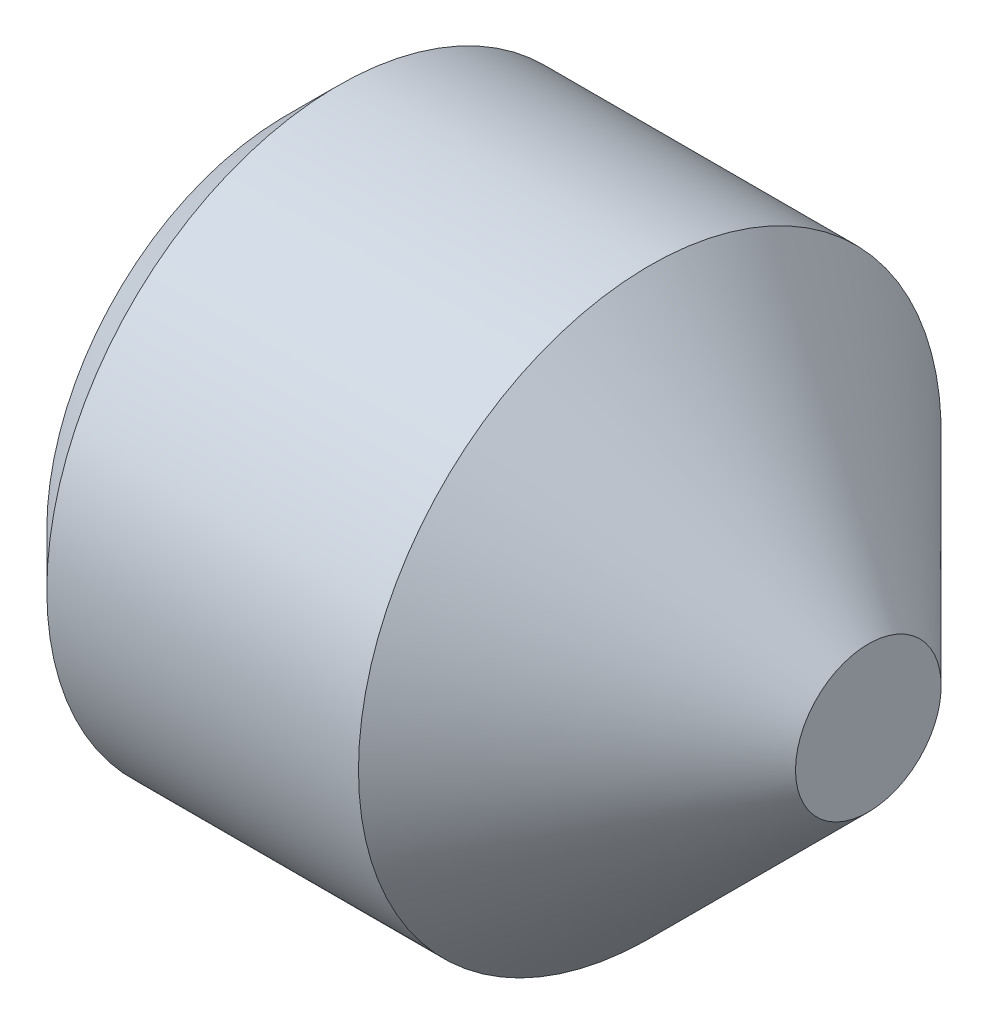
SolidWorks part; units mm, degrees
ref_plane "Front" through (0, 0, 0) normal (0, 0, 1) x (1, 0, 0)
ref_plane "Top" through (0, 0, 0) normal (0, 1, 0) x (1, 0, 0)
ref_plane "Right" through (0, 0, 0) normal (1, 0, 0) x (0, 0, -1)
sketch "Sketch1" plane through (0, 0, 0) normal (0, 0, 1) x (1, 0, 0)
  line L0 (0, 0) -> (3, 0)
  line L1 (3, 0) -> (3, 0.375)
  line L2 (3, 0.375) -> (1.875, 1.5)
  line L3 (1.875, 1.5) -> (0.2705, 1.5)
  line L4 (0.2705, 1.5) -> (0, 1.2295)
  line L5 (0, 1.2295) -> (0, 0)
  line L6 (-14.7741, 0) -> (12.5137, 0) construction
  dimension "l" = 3
  dimension "dt" = 0.75
  dimension "d" = 3
  dimension "df" = 2.459
  dimension "D1" = 45
  dimension "D2" = 45
revolve "Base" add sketch "Sketch1" angle 360 about L6
cosmetic thread "ThreadCosmetic1" [suppressed] parameters "D2"=2.459
sketch "Sketch2" plane through (0, 0.2203, -0.1392) normal (-1, 0, 0) x (0, 0, 1)
  line L1 (1.0052, -0.2203) -> (0.5722, 0.5297)
  line L2 (0.5722, 0.5297) -> (-0.2938, 0.5297)
  line L3 (-0.2938, 0.5297) -> (-0.7268, -0.2203)
  line L4 (-0.7268, -0.2203) -> (-0.2938, -0.9703)
  line L5 (-0.2938, -0.9703) -> (0.5722, -0.9703)
  line L6 (0.5722, -0.9703) -> (1.0052, -0.2203)
  circle A0 centre (0.1392, -0.2203) radius 0.75 construction
  dimension "s" = 1.5
extrude "HexagonSocket" cut sketch "Sketch2" against normal blind 1.2
sketch "Sketch3" plane through (0, 0, 0) normal (0, 0, 1) x (1, 0, 0)
  line L0 (1.2, 0) -> (-2.4777, 0) construction
  line L2 (1.2, 0.75) -> (1.633, 0)
  line L3 (1.633, 0) -> (1.2, -0.75) construction
  line L4 (1.2, 0.75) -> (1.2, 0)
  line L5 (1.2, 0) -> (1.633, 0)
  dimension "D1" = 120
revolve "Cut-Revolve" cut sketch "Sketch3" angle 360 about L0
sketch "Sketch4" plane through (0, 0, 0) normal (0, 0, 1) x (1, 0, 0)
  line L0 (0.2705, 1.2657) -> (0.4058, 1.5)
  line L1 (0.4058, 1.5) -> (0.4058, 1.7705)
  line L2 (0.4058, 1.7705) -> (0.1353, 1.7705)
  line L3 (0.1353, 1.7705) -> (0.1353, 1.5)
  line L4 (0.1353, 1.5) -> (0.2705, 1.2657)
  line L5 (0, 0) -> (3.2295, 0) construction
  line L6 (0.2705, 1.5) -> (0.2705, -1.5) construction
  dimension "D1" = 3
  dimension "D2" = 0.2705
revolve "Cut-Revolve10" [suppressed] cut sketch "Sketch4" angle 360 about L5
pattern_linear "LPattern10" [suppressed] count 9 spacing 0.3246 along (1, 0, 0)
equation "\"df@Sketch1\" = \"D2@ThreadCosmetic1\""
equation "\"D1@Sketch4\" = \"d@Sketch1\""
equation "\"D2@Sketch4\" =  ( \"d@Sketch1\" - \"D2@ThreadCosmetic1\" )  / 2"
equation "\"D3@LPattern10\" = \"D2@Sketch4\" * 1.2"
equation "\"D1@LPattern10\" = \"l@Sketch1\" / \"D3@LPattern10\""
